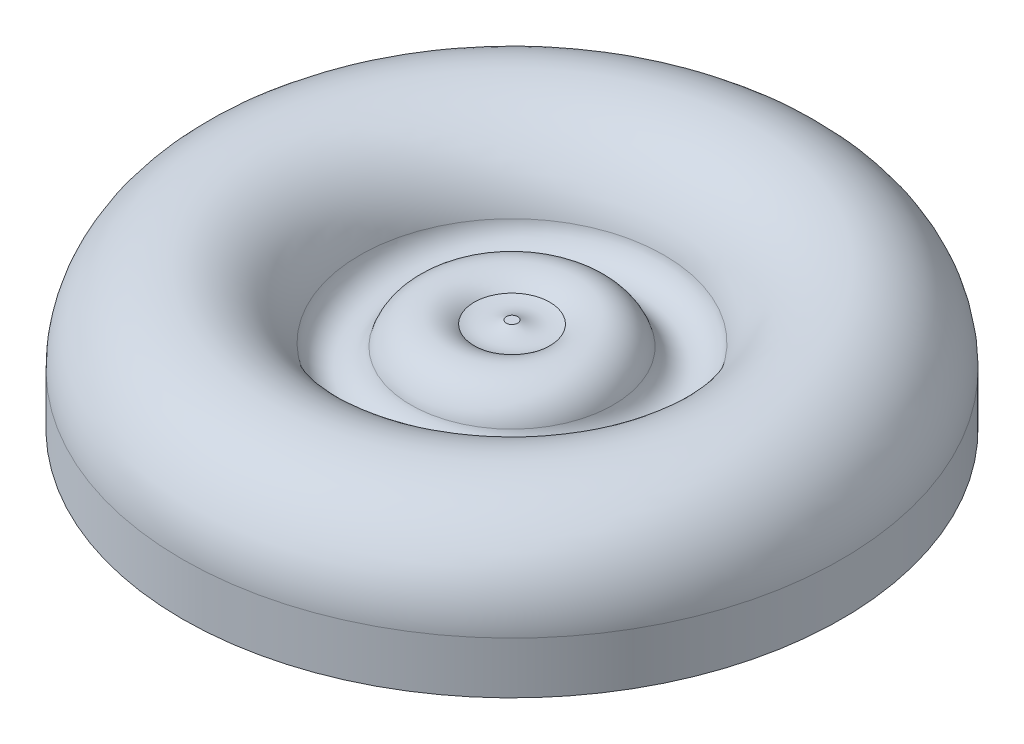
SolidWorks part; units mm, degrees
ref_plane "Front Plane" through (0, 0, 0) normal (0, 0, 1) x (1, 0, 0)
ref_plane "Top Plane" through (0, 0, 0) normal (0, 1, 0) x (1, 0, 0)
ref_plane "Right Plane" through (0, 0, 0) normal (1, 0, 0) x (0, 0, -1)
sketch "Sketch1" plane through (0, 0, 0) normal (0, 0, 1) x (1, 0, 0)
  line L0 (0, 0) -> (0, 7.1402)
  line L1 (0, 0) -> (-45.466, 0)
  line L2 (-45.466, 0) -> (-45.466, 13.0196)
  line L3 (-45.466, 13.0196) -> (-44.6786, 13.0196)
  arc A0 (0, 7.1402) -> (-24.4896, 10.2795) centre (-12.446, 7.1402) ccw
  arc A1 (-31.5019, 9.8283) -> (-24.4896, 10.2795) centre (-28.0549, 10.9733) ccw
  arc A2 (-31.5019, 9.8283) -> (-40.2544, 12.5306) centre (-36.7417, 8.3825) ccw
  arc A3 (-44.6786, 13.0196) -> (-40.2544, 12.5306) centre (-41.8852, 18.0345) ccw
revolve "Revolve1" add sketch "Sketch1" angle 360 about L2
